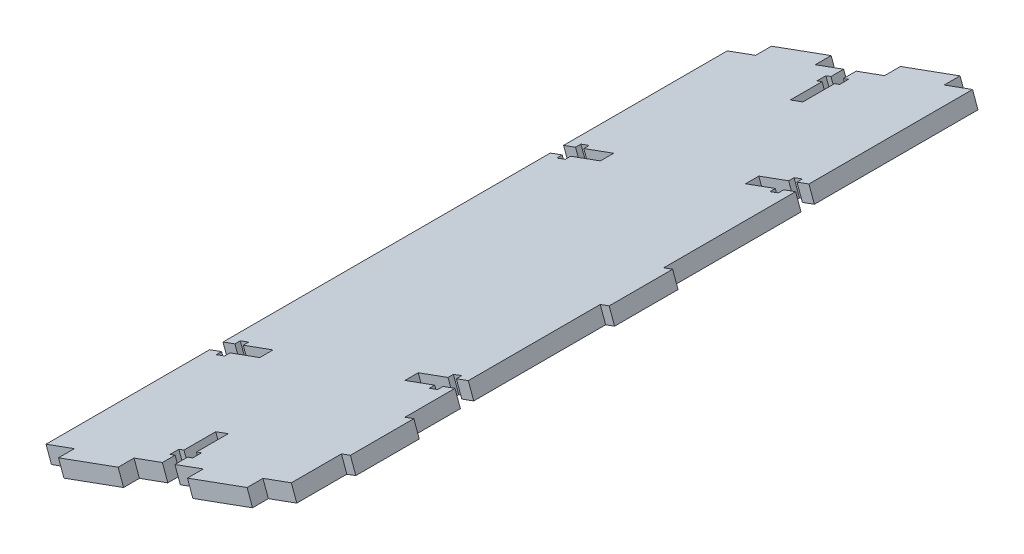
SolidWorks part; units mm, degrees
ref_plane "Front Plane" through (0, 0, 0) normal (0, 0, 1) x (1, 0, 0)
ref_plane "Top Plane" through (0, 0, 0) normal (0, 1, 0) x (1, 0, 0)
ref_plane "Right Plane" through (0, 0, 0) normal (1, 0, 0) x (0, 0, -1)
sketch "Sketch2" plane through (0, 0, 4.9494) normal (0, 0, 1) x (1, 0, 0)
  line L12 (-59.322, -39.1751) -> (-151.1595, -72.5724) construction
  line L17 (-52.9615, -36.8621) -> (-51.2527, -41.561)
  line L18 (-52.9615, -36.8621) -> (-130.276, -64.978)
  line L19 (-51.2527, -41.561) -> (-128.5672, -69.6769)
  line L20 (-130.276, -64.978) -> (-128.5672, -69.6769)
  line L24 (-119.7019, -94.055) -> (-108.4238, -125.068) construction
  dimension "D1" = 5
extrude "Boss-Extrude1" add sketch "Sketch2" along normal up to surface (214.6865 mm away)
sketch "Sketch4" plane through (7.3623, -20.2452, 0) normal (0.3418, -0.9398, 0) x (-0.9398, -0.3418, 0)
  line L0 (101.4046, -4.9494) -> (105.6046, -4.9494)
  line L1 (101.4046, -4.9494) -> (101.4046, -8.9494)
  line L2 (105.6046, -4.9494) -> (105.6046, -8.9494)
  line L3 (99.7046, -8.9494) -> (101.4046, -8.9494)
  line L4 (99.7046, -8.9494) -> (99.7046, -11.7494)
  line L5 (107.3046, -8.9494) -> (107.3046, -11.7494)
  line L6 (99.7046, -11.7494) -> (101.4046, -11.7494)
  line L7 (101.4046, -11.7494) -> (101.4046, -21.7494)
  line L8 (105.6046, -11.7494) -> (105.6046, -21.7494)
  line L9 (101.4046, -21.7494) -> (105.6046, -21.7494)
  line L10 (105.6046, -11.7494) -> (107.3046, -11.7494)
  line L11 (105.6046, -8.9494) -> (107.3046, -8.9494)
  line L14 (62.3706, -60.721) -> (62.3706, -56.521)
  line L25 (62.3706, -4.9494) -> (144.6386, -4.9494) construction
  line L26 (105.6046, -219.6358) -> (101.4046, -219.6358)
  line L27 (105.6046, -219.6358) -> (105.6046, -215.6358)
  line L28 (103.5046, -21.7494) -> (103.5046, -4.9494) construction
  line L29 (101.4046, -219.6358) -> (101.4046, -215.6358)
  line L30 (107.3046, -215.6358) -> (105.6046, -215.6358)
  line L31 (107.3046, -215.6358) -> (107.3046, -212.8358)
  line L32 (99.7046, -215.6358) -> (99.7046, -212.8358)
  line L33 (107.3046, -212.8358) -> (105.6046, -212.8358)
  line L34 (105.6046, -212.8358) -> (105.6046, -202.8358)
  line L35 (101.4046, -212.8358) -> (101.4046, -202.8358)
  line L36 (105.6046, -202.8358) -> (101.4046, -202.8358)
  line L37 (101.4046, -212.8358) -> (99.7046, -212.8358)
  line L38 (101.4046, -215.6358) -> (99.7046, -215.6358)
  line L39 (103.5046, -202.8358) -> (103.5046, -219.6358) construction
  line L40 (62.3706, -219.6358) -> (144.6386, -219.6358) construction
  line L41 (62.3706, -60.721) -> (66.3706, -60.721)
  line L42 (62.3706, -56.521) -> (66.3706, -56.521)
  line L43 (66.3706, -62.421) -> (66.3706, -60.721)
  line L44 (66.3706, -62.421) -> (69.1706, -62.421)
  line L45 (66.3706, -54.821) -> (69.1706, -54.821)
  line L46 (69.1706, -62.421) -> (69.1706, -60.721)
  line L47 (69.1706, -60.721) -> (79.1706, -60.721)
  line L48 (69.1706, -56.521) -> (79.1706, -56.521)
  line L49 (79.1706, -60.721) -> (79.1706, -56.521)
  line L50 (69.1706, -56.521) -> (69.1706, -54.821)
  line L51 (66.3706, -56.521) -> (66.3706, -54.821)
  line L52 (79.1706, -58.621) -> (62.3706, -58.621) construction
  line L55 (62.3706, -219.6358) -> (62.3706, -4.9494) construction
  line L56 (62.3706, -4.9494) -> (62.3706, -112.2926) construction
  line L57 (62.3706, -112.2926) -> (144.6386, -112.2926) construction
  line L58 (79.1706, -165.9642) -> (62.3706, -165.9642) construction
  line L59 (66.3706, -168.0642) -> (66.3706, -169.7642)
  line L60 (69.1706, -168.0642) -> (69.1706, -169.7642)
  line L61 (79.1706, -163.8642) -> (79.1706, -168.0642)
  line L62 (69.1706, -168.0642) -> (79.1706, -168.0642)
  line L63 (69.1706, -163.8642) -> (79.1706, -163.8642)
  line L64 (69.1706, -162.1642) -> (69.1706, -163.8642)
  line L65 (66.3706, -169.7642) -> (69.1706, -169.7642)
  line L66 (66.3706, -162.1642) -> (69.1706, -162.1642)
  line L67 (66.3706, -162.1642) -> (66.3706, -163.8642)
  line L68 (62.3706, -168.0642) -> (66.3706, -168.0642)
  line L69 (62.3706, -163.8642) -> (66.3706, -163.8642)
  line L70 (62.3706, -163.8642) -> (62.3706, -168.0642)
  line L76 (144.6386, -219.6358) -> (144.6386, -4.9494) construction
  line L77 (103.5046, -171.4513) -> (103.5046, -40.1199) construction
  line L78 (127.8386, -165.9642) -> (144.6386, -165.9642) construction
  line L87 (144.6386, -4.9494) -> (144.6386, -112.2926) construction
  line L88 (127.8386, -58.621) -> (144.6386, -58.621) construction
  line L89 (144.6386, -163.8642) -> (144.6386, -168.0642)
  line L90 (144.6386, -163.8642) -> (140.6386, -163.8642)
  line L91 (144.6386, -168.0642) -> (140.6386, -168.0642)
  line L92 (140.6386, -162.1642) -> (140.6386, -163.8642)
  line L93 (140.6386, -162.1642) -> (137.8386, -162.1642)
  line L94 (140.6386, -169.7642) -> (137.8386, -169.7642)
  line L95 (137.8386, -162.1642) -> (137.8386, -163.8642)
  line L96 (137.8386, -163.8642) -> (127.8386, -163.8642)
  line L97 (137.8386, -168.0642) -> (127.8386, -168.0642)
  line L98 (127.8386, -163.8642) -> (127.8386, -168.0642)
  line L99 (137.8386, -168.0642) -> (137.8386, -169.7642)
  line L100 (140.6386, -168.0642) -> (140.6386, -169.7642)
  line L101 (140.6386, -56.521) -> (140.6386, -54.821)
  line L102 (137.8386, -56.521) -> (137.8386, -54.821)
  line L103 (127.8386, -60.721) -> (127.8386, -56.521)
  line L104 (137.8386, -56.521) -> (127.8386, -56.521)
  line L105 (137.8386, -60.721) -> (127.8386, -60.721)
  line L106 (137.8386, -62.421) -> (137.8386, -60.721)
  line L107 (140.6386, -54.821) -> (137.8386, -54.821)
  line L108 (140.6386, -62.421) -> (137.8386, -62.421)
  line L109 (140.6386, -62.421) -> (140.6386, -60.721)
  line L110 (144.6386, -56.521) -> (140.6386, -56.521)
  line L111 (144.6386, -60.721) -> (140.6386, -60.721)
  line L112 (144.6386, -60.721) -> (144.6386, -56.521)
  point P70 (103.5046, -112.2926)
  dimension "D1" = 4.2
  dimension "D2" = 1.7
  dimension "D3" = 1.7
  dimension "D4" = 2.8
  dimension "D5" = 10
  dimension "D6" = 4
  dimension "D7" = 4.2
  dimension "D8" = 1.7
  dimension "D9" = 1.7
  dimension "D10" = 2.8
  dimension "D11" = 10
  dimension "D12" = 4
  dimension "D13" = 4.2
  dimension "D14" = 1.7
  dimension "D15" = 1.7
  dimension "D16" = 2.8
  dimension "D17" = 10
  dimension "D18" = 4
extrude "Cut-Extrude3" cut sketch "Sketch4" against normal through all
sketch "Sketch5" plane through (7.3623, -20.2452, 0) normal (0.3418, -0.9398, 0) x (0.9398, 0.3418, 0)
  line L0 (-115.1216, 219.6358) -> (-135.1216, 219.6358)
  line L1 (-115.1216, 219.6358) -> (-115.1216, 224.6358)
  line L2 (-135.1216, 219.6358) -> (-135.1216, 224.6358)
  line L3 (-115.1216, 224.6358) -> (-135.1216, 224.6358)
  line L4 (-144.6386, 219.6358) -> (-105.6046, 219.6358) construction
  line L5 (-71.8876, 219.6358) -> (-91.8876, 219.6358)
  line L6 (-71.8876, 219.6358) -> (-71.8876, 224.6358)
  line L7 (-91.8876, 219.6358) -> (-91.8876, 224.6358)
  line L8 (-71.8876, 224.6358) -> (-91.8876, 224.6358)
  line L9 (-101.4046, 219.6358) -> (-62.3706, 219.6358) construction
  line L10 (-62.3706, 102.2926) -> (-62.3706, 122.2926)
  line L11 (-62.3706, 102.2926) -> (-59.3706, 102.2926)
  line L12 (-62.3706, 122.2926) -> (-59.3706, 122.2926)
  line L13 (-59.3706, 102.2926) -> (-59.3706, 122.2926)
  line L14 (-62.3706, 60.721) -> (-62.3706, 163.8642) construction
  line L15 (-62.3706, 203.85) -> (-62.3706, 183.85)
  line L16 (-62.3706, 203.85) -> (-59.3706, 203.85)
  line L17 (-62.3706, 183.85) -> (-59.3706, 183.85)
  line L18 (-59.3706, 203.85) -> (-59.3706, 183.85)
  line L19 (-62.3706, 168.0642) -> (-62.3706, 219.6358) construction
  line L20 (-62.3706, 425.3148) -> (-62.3706, -200.7297)
  line L24 (-62.3706, 60.721) -> (-62.3706, 163.8642) construction
  line L25 (-135.1216, 4.9494) -> (-115.1216, 4.9494)
  line L26 (-135.1216, 4.9494) -> (-135.1216, -0.0506)
  line L27 (-115.1216, 4.9494) -> (-115.1216, -0.0506)
  line L28 (-135.1216, -0.0506) -> (-115.1216, -0.0506)
  line L29 (-144.6386, 4.9494) -> (-105.6046, 4.9494) construction
  line L30 (-91.8876, 4.9494) -> (-71.8876, 4.9494)
  line L31 (-91.8876, 4.9494) -> (-91.8876, -0.0506)
  line L32 (-71.8876, 4.9494) -> (-71.8876, -0.0506)
  line L33 (-91.8876, -0.0506) -> (-71.8876, -0.0506)
  line L34 (-101.4046, 4.9494) -> (-62.3706, 4.9494) construction
  line L35 (25.2614, 224.6358) -> (-232.1386, 224.6358) construction
  point P10 (-125.1216, 219.6358)
  point P11 (-81.8876, 219.6358)
  point P16 (-62.3706, 112.2926)
  point P23 (-62.3706, 193.85)
  point P31 (-62.3706, 112.2926)
  point P39 (-125.1216, 4.9494)
  point P49 (-81.8876, 4.9494)
  dimension "D2" = 20
  dimension "D4" = 20
  dimension "D5" = 3
  dimension "D6" = 20
  dimension "D7" = 3
  dimension "D8" = 20
  dimension "D11" = 5
  dimension "D12" = 20
  dimension "D13" = 5
  dimension "D14" = 20
extrude "Boss-Extrude2" add sketch "Sketch5" against normal blind 5 contours L31 L33 L32 L30 | L26 L28 L27 L25 | L11 L13 L12 L10 | L18 L16 L15 L17 | L6 L8 L7 L5 | L1 L3 L2 L0
